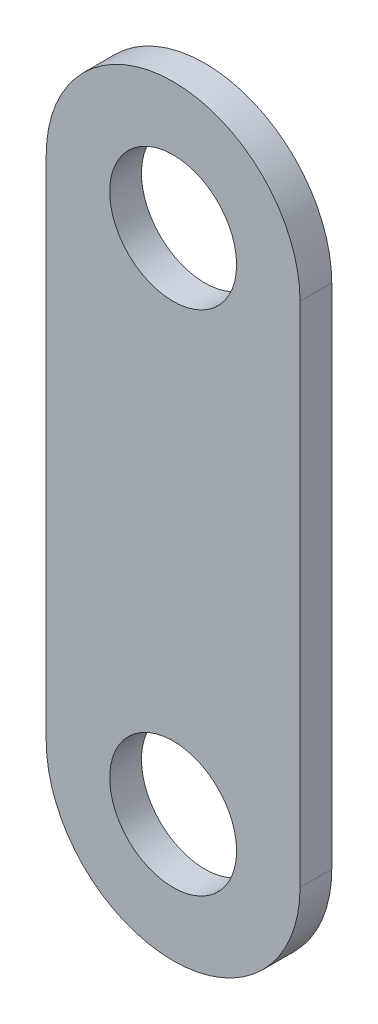
SolidWorks part; units mm, degrees
ref_plane "Front" through (0, 0, 0) normal (0, 0, 1) x (1, 0, 0)
ref_plane "Top" through (0, 0, 0) normal (0, 1, 0) x (1, 0, 0)
ref_plane "Right" through (0, 0, 0) normal (1, 0, 0) x (0, 0, -1)
sketch "Sketch1" plane through (0, 0, 0) normal (0, 0, 1) x (1, 0, 0)
  line L0 (-29.9132, -25.0577) -> (-29.9132, 25.7423)
  line L1 (-4.5132, 25.7423) -> (-4.5132, -25.0577)
  circle A0 centre (-17.2132, 25.7423) radius 12.7
  circle A1 centre (-17.2132, -25.0577) radius 12.7
  circle A2 centre (-17.2132, 25.7423) radius 6.35
  circle A3 centre (-17.2132, -25.0577) radius 6.35
  point P8 (-4.5132, 0.3423)
  dimension "D1" = 50.8
  dimension "D3" = 12.7
  dimension "D4" = 12.7
  dimension "D2" = 25.4
extrude "Boss-Extrude1" add sketch "Sketch1" along normal blind 3.175 contours A0 A2 | A1 L1 A0 L0 | A1 A3
